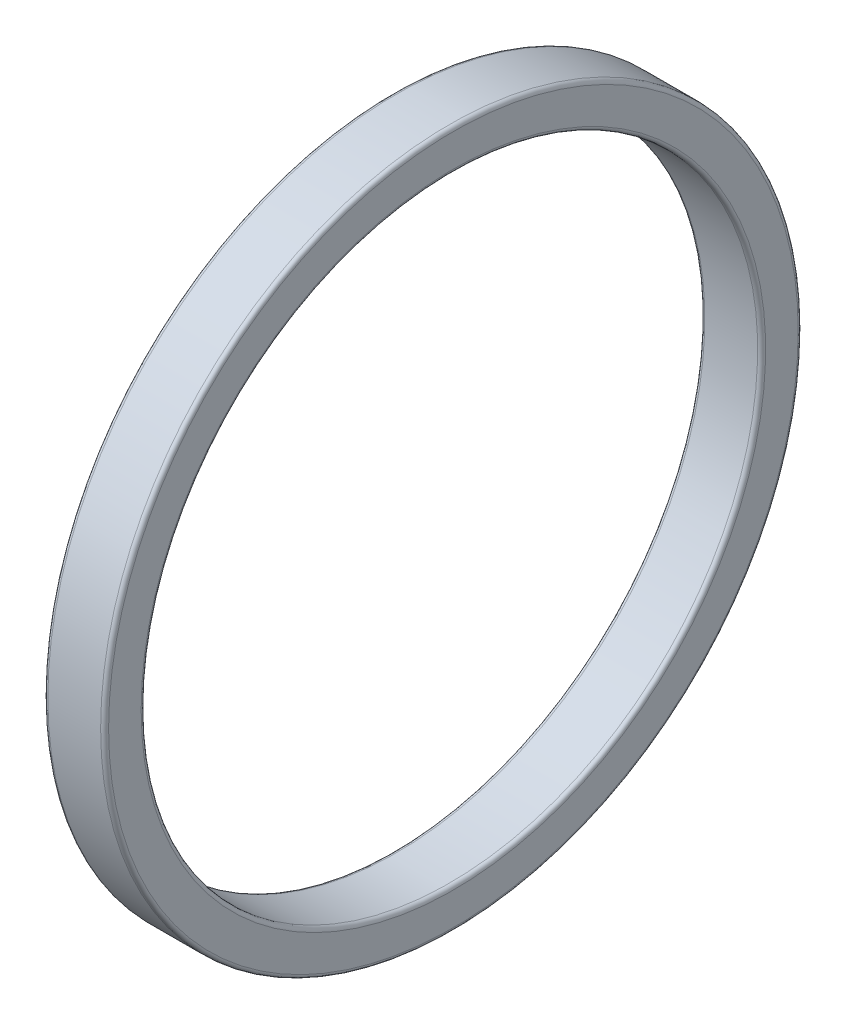
SolidWorks part; units mm, degrees
ref_plane "Front Plane" through (0, 0, 0) normal (0, 0, 1) x (1, 0, 0)
ref_plane "Top Plane" through (0, 0, 0) normal (0, 1, 0) x (1, 0, 0)
ref_plane "Right Plane" through (0, 0, 0) normal (1, 0, 0) x (0, 0, -1)
sketch "Sketch2" plane through (0, 0, 0) normal (0, 0, 1) x (1, 0, 0)
  line L0 (-279.6154, -15.4572) -> (-279.6154, 15.4572) construction
  line L1 (-279.4154, 15.4572) -> (-276.7674, 15.4572)
  line L2 (-279.6154, 15.6572) -> (-279.6154, 17.2892)
  line L3 (-279.4154, 17.4892) -> (-276.7674, 17.4892)
  line L4 (-276.5674, 15.6572) -> (-276.5674, 17.2892)
  line L5 (-279.6154, -17.4892) -> (-279.6154, 17.4892) construction
  line L6 (-276.5674, 17.4892) -> (-276.5674, -17.4892) construction
  line L7 (-295.3116, 0) -> (-273.5688, 0) construction
  arc A0 (-276.7674, 17.4892) -> (-276.5674, 17.2892) centre (-276.7674, 17.2892) cw
  arc A1 (-276.5674, 15.6572) -> (-276.7674, 15.4572) centre (-276.7674, 15.6572) cw
  arc A2 (-279.4154, 15.4572) -> (-279.6154, 15.6572) centre (-279.4154, 15.6572) cw
  arc A3 (-279.6154, 17.2892) -> (-279.4154, 17.4892) centre (-279.4154, 17.2892) cw
  point P12 (-276.5674, 17.4892)
  point P17 (-279.6154, 15.4572)
  dimension "D1" = 0.2
revolve "Revolve1" add sketch "Sketch2" angle 360 about L7
